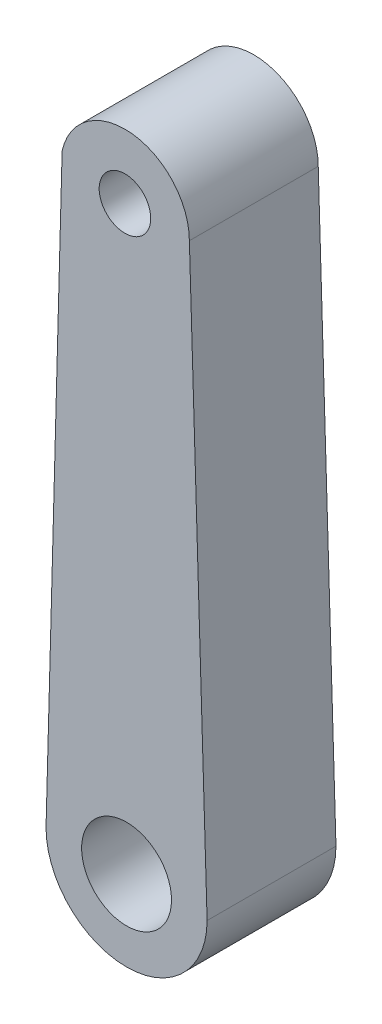
SolidWorks part; units mm, degrees
material "Alloy Steel"
ref_plane "Front Plane" through (0, 0, 0) normal (0, 0, 1) x (1, 0, 0)
ref_plane "Top Plane" through (0, 0, 0) normal (0, 1, 0) x (1, 0, 0)
ref_plane "Right Plane" through (0, 0, 0) normal (1, 0, 0) x (0, 0, -1)
other "Configuration Table"
sketch "Sketch2" plane through (0, 0, 0) normal (0, 0, 1) x (1, 0, 0)
  line L0 (-12.5, 0) -> (-10, 92.2329)
  line L2 (12.5, 0) -> (9.7474, 89.9996)
  arc A0 (-12.5, 0) -> (12.5, 0) centre (0, 0) ccw
  arc A1 (-10, 92.2329) -> (9.7474, 89.9996) centre (-0.2526, 89.9996) cw
  dimension "D1" = 12.5
  dimension "D2" = 10
  dimension "D3" = 90
extrude "Extrude1" add sketch "Sketch2" along normal mid plane 20
sketch "Sketch6" plane through (0, 0, 10) normal (0, 0, 1) x (1, 0, 0)
  circle A0 centre (-0.2526, 89.9996) radius 4
  dimension "D1" = 8
extrude "Cut-Extrude1" cut sketch "Sketch6" against normal through all
sketch "Sketch3" plane through (0, 0, 0) normal (0, 1, 0) x (1, 0, 0)
  line L0 (-10, 0) -> (9.7474, 0)
  line L3 (-10, -10) -> (-10, 10) construction
  line L4 (9.7474, -10) -> (9.7474, 10) construction
split line "Split Line1" [suppressed]
sketch "Sketch8" plane through (0, 0, 10) normal (0, 0, 1) x (1, 0, 0)
  circle A0 centre (0, 0) radius 6.975
  dimension "D1" = 13.95
extrude "Cut-Extrude2" cut sketch "Sketch8" against normal through all
sketch "Sketch5" plane through (0, 0, 0) normal (0, 1, 0) x (1, 0, 0)
  line L0 (-10, 0) -> (9.6591, 0)
  line L3 (-10, -10) -> (-10, 10) construction
split line "Split Line2" [suppressed]
